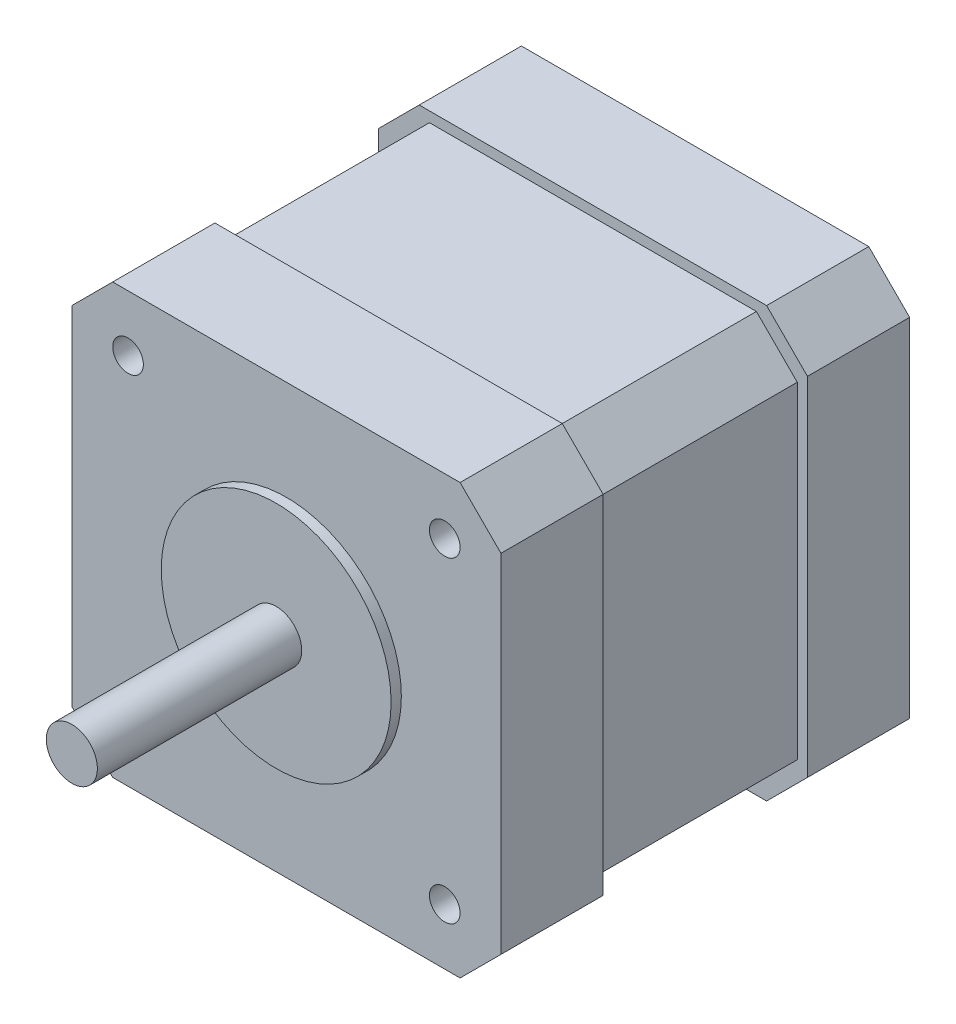
SolidWorks part; units mm, degrees
ref_plane "Front Plane" through (0, 0, 0) normal (0, 0, 1) x (1, 0, 0)
ref_plane "Top Plane" through (0, 0, 0) normal (0, 1, 0) x (1, 0, 0)
ref_plane "Right Plane" through (0, 0, 0) normal (1, 0, 0) x (0, 0, -1)
sketch "Sketch1" plane through (0, 0, 0) normal (0, 0, 1) x (1, 0, 0)
  line L1 (-21, 21) -> (21, 21)
  line L2 (-21, 21) -> (-21, -21)
  line L3 (-21, -21) -> (21, -21)
  line L4 (21, 21) -> (21, -21)
  line L5 (-21, 21) -> (21, -21) construction
  line L6 (-21, -21) -> (21, 21) construction
  point P0 (0, 0)
  dimension "D1" = 42
  dimension "D2" = 42
extrude "Boss-Extrude1" add sketch "Sketch1" along normal blind 10
sketch "Sketch2" plane through (0, 0, 10) normal (0, 0, 1) x (1, 0, 0)
  line L1 (-20, 20) -> (20, 20)
  line L2 (-20, 20) -> (-20, -20)
  line L3 (-20, -20) -> (20, -20)
  line L4 (20, 20) -> (20, -20)
  line L5 (-20, 20) -> (20, -20) construction
  line L6 (-20, -20) -> (20, 20) construction
  point P0 (0, 0)
  dimension "D1" = 40
  dimension "D2" = 40
extrude "Boss-Extrude2" add sketch "Sketch2" along normal blind 20
sketch "Sketch3" plane through (0, 0, 30) normal (0, 0, 1) x (1, 0, 0)
  line L1 (-21, 21) -> (21, 21)
  line L2 (-21, 21) -> (-21, -21)
  line L3 (-21, -21) -> (21, -21)
  line L4 (21, 21) -> (21, -21)
  line L5 (-21, 21) -> (21, -21) construction
  line L6 (-21, -21) -> (21, 21) construction
  point P0 (0, 0)
  dimension "D1" = 42
  dimension "D2" = 42
extrude "Boss-Extrude3" add sketch "Sketch3" along normal blind 10
sketch "Sketch4" plane through (0, 0, 40) normal (0, 0, 1) x (1, 0, 0)
  circle A0 centre (0, 0) radius 11.25
  dimension "D1" = 22.5
extrude "Boss-Extrude4" add sketch "Sketch4" along normal blind 1
chamfer "Chamfer1" distance 4 angle 45 12 edges at (-21, -21, 35) (-20, -20, 20) (-21, -21, 5) (21, -21, 35) (20, -20, 20) (21, -21, 5) (21, 21, 35) (20, 20, 20) (21, 21, 5) (-21, 21, 35) (-20, 20, 20) (-21, 21, 5)
sketch "Sketch5" plane through (0, 0, 41) normal (0, 0, 1) x (1, 0, 0)
  circle A0 centre (0, 0) radius 2.5
  dimension "D1" = 5
extrude "Boss-Extrude5" add sketch "Sketch5" along normal blind 20
sketch "Sketch6" plane through (0, 0, 40) normal (0, 0, 1) x (1, 0, 0)
  line L1 (-15.5, -15.5) -> (15.5, -15.5) construction
  line L2 (-15.5, -15.5) -> (-15.5, 15.5) construction
  line L3 (-15.5, 15.5) -> (15.5, 15.5) construction
  line L4 (15.5, -15.5) -> (15.5, 15.5) construction
  line L5 (-15.5, -15.5) -> (15.5, 15.5) construction
  line L6 (-15.5, 15.5) -> (15.5, -15.5) construction
  circle A0 centre (-15.5, -15.5) radius 1.5
  circle A1 centre (-15.5, 15.5) radius 1.5
  circle A2 centre (15.5, 15.5) radius 1.5
  circle A3 centre (15.5, -15.5) radius 1.5
  point P8 (0, 0)
  dimension "D8" = 3
  dimension "D9" = 3
  dimension "D10" = 3
  dimension "D11" = 3
  dimension "D1" = 31
  dimension "D4" = 31
extrude "Cut-Extrude1" cut sketch "Sketch6" against normal blind 40
